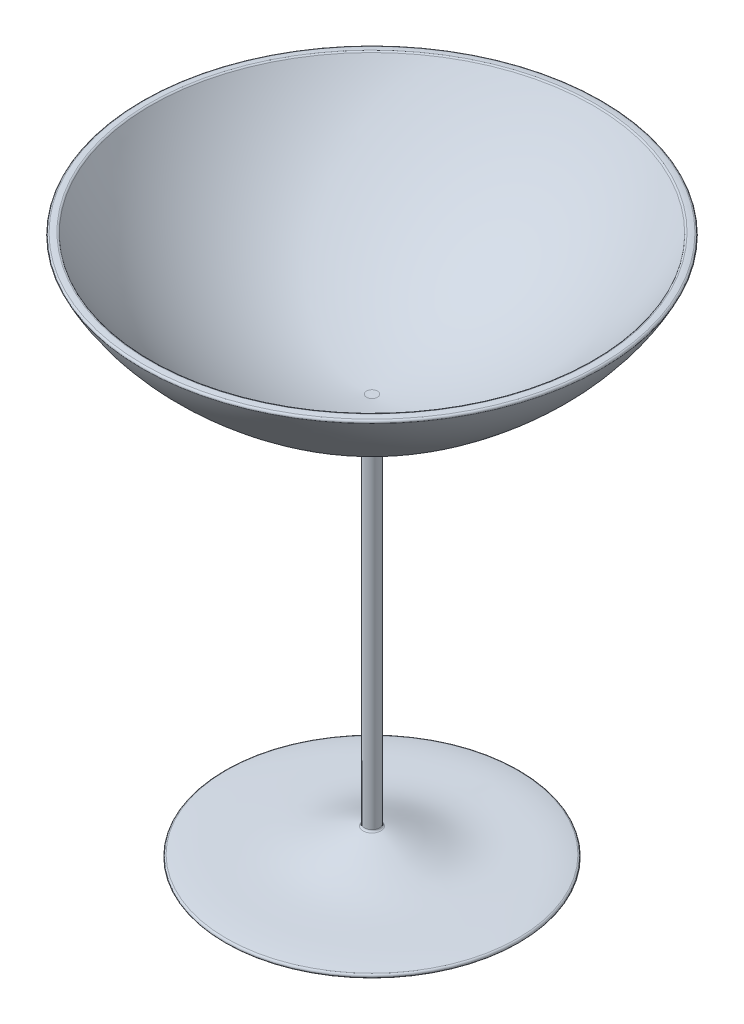
SolidWorks part; units mm, degrees
ref_plane "Front Plane" through (0, 0, 0) normal (0, 0, 1) x (1, 0, 0)
ref_plane "Top Plane" through (0, 0, 0) normal (0, 1, 0) x (1, 0, 0)
ref_plane "Right Plane" through (0, 0, 0) normal (1, 0, 0) x (0, 0, -1)
sketch "Sketch1" plane through (0, 0, 0) normal (0, 0, 1) x (1, 0, 0)
  line L0 (0, 0) -> (0, 46.4831) construction
  line L5 (-1.8866, 0) -> (-1.8866, -94.6128)
  line L6 (0, 0) -> (0, -101.9937) construction
  line L7 (-40.946, -101.9937) -> (-18.9765, -101.9937)
  line L8 (0, 0.4578) -> (0, -96.9918)
  spline S0 degree 3 poles (-1.8866, 0) (-9.704, 0.4588) (-23.8503, 4.0067) (-43.4089, 16.716) (-54.8437, 27.8217) (-58.81, 35.9344) knots 0 0 0 0 0.337374 0.612445 1 1 1 1
  spline S1 degree 3 poles (-58.81, 35.9344) (-58.4291, 35.9981) (-57.6428, 36.1299) (-56.8472, 36.2215) (-56.4345, 36.2012) knots 0 0 0 0 0.483682 1 1 1 1
  spline S2 degree 3 poles (-18.9765, -101.9937) (-15.1714, -101.8845) (-8.8865, -99.8982) (-2.7648, -97.5004) (0, -96.9918) knots 0 0 0 0 0.572893 1 1 1 1
  spline S3 degree 3 poles (-1.8866, -94.6128) (-6.8316, -95.8915) (-19.071, -102.3721) (-33.1185, -99.2815) (-40.946, -101.9937) knots 0 0 0 0 0.386922 1 1 1 1
  spline S5 degree 3 poles (-1.3866, 0.4578) (-1.4994, 0.4678) (-1.6924, 0.4849) (-3.1145, 0.6096) (-5.8415, 0.9384) (-11.2281, 1.9643) (-18.0072, 3.9798) (-25.7599, 7.4177) (-35.5086, 13.2142) (-44.2365, 20.617) (-51.6884, 29.2147) (-54.9309, 33.8186) (-56.4345, 36.2012) knots -0.006652 -0.006652 -0.006652 -0.006652 -0.001663 0.001663 0.056264 0.11918 0.245011 0.370843 0.496674 0.748337 0.874169 1 1 1 1
  spline S9 degree 3 poles (-1.3866, 0.4578) (-0.9254, 0.4198) (-0.4615, 0.4306) (0, 0.4578) knots 0 0 0 0 1 1 1 1
revolve "Revolve2" add sketch "Sketch1" angle 360 about L0
fillet "Fillet1" radius 0.5 2 edges at (0, 36.2012, -56.4345) (0, 35.9344, -58.81)
fillet "Fillet2" radius 0.5 3 edges at (0, 0, -1.8866) (0, -94.6128, -1.8866) (0, -101.9937, -40.946)
